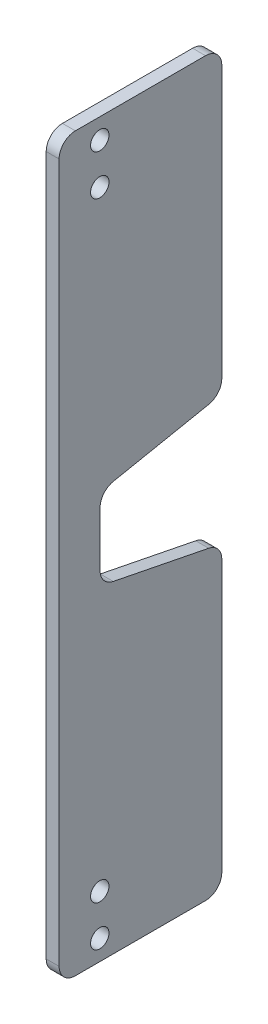
SolidWorks part; units mm, degrees
ref_plane "前视基准面" through (0, 0, 0) normal (0, 0, 1) x (1, 0, 0)
ref_plane "上视基准面" through (0, 0, 0) normal (0, 1, 0) x (1, 0, 0)
ref_plane "右视基准面" through (0, 0, 0) normal (1, 0, 0) x (0, 0, -1)
ref_plane "基准面4" through (-0.7938, 0, 0) normal (-1, 0, 0) x (0, -1, 0)
sketch "草图1" plane through (-0.7938, 0, 0) normal (-1, 0, 0) x (0, -1, 0)
  line L1 (38.795, 5) -> (12.795, 5)
  line L2 (10.795, 3) -> (10.795, -13)
  line L5 (10.795, 3) -> (55.77, 3) construction
  line L6 (55.77, 3) -> (55.77, -5.0783) construction
  line L7 (55.77, 3) -> (55.77, 5) construction
  line L13 (38.795, 5) -> (72.745, 5)
  line L15 (100.745, 3) -> (100.745, -13)
  line L18 (72.745, 5) -> (98.745, 5)
  line L19 (55.77, 5) -> (55.77, -5.0783) construction
  line L20 (55.77, -5.0783) -> (55.77, -0.0391) construction
  line L21 (55.77, -0.0391) -> (65.77, -0.0391) construction
  line L22 (72.112, -14.1547) -> (62.1308, -0.0391) construction
  line L31 (12.795, -15) -> (47.795, -15)
  line L32 (55.77, -0.0391) -> (50.77, -0.0391)
  line L33 (55.77, -0.0391) -> (60.77, -0.0391)
  line L34 (98.745, -15) -> (63.745, -15)
  line L37 (50.77, -0.0391) -> (47.795, -15)
  line L38 (60.77, -0.0391) -> (63.745, -15)
  arc A2 (12.795, 5) -> (10.795, 3) centre (12.795, 3) ccw
  arc A3 (10.795, -13) -> (12.795, -15) centre (12.795, -13) ccw
  circle A5 centre (18.295, 0) radius 1.1303
  circle A6 centre (13.295, 0) radius 1.1303
  arc A12 (98.745, 5) -> (100.745, 3) centre (98.745, 3) cw
  arc A13 (100.745, -13) -> (98.745, -15) centre (98.745, -13) cw
  circle A14 centre (98.245, 0) radius 1.1303
  circle A15 centre (93.245, 0) radius 1.1303
extrude "凸台-拉伸1" add sketch "草图1" against normal blind 1.588
fillet "圆角1" radius 2 1 edges at (0.0002, -50.77, -0.0391)
fillet "圆角2" radius 2 1 edges at (0.0003, -47.795, -15)
fillet "圆角3" radius 2 1 edges at (0.0002, -60.77, -0.0391)
fillet "圆角4" radius 2 1 edges at (0.0003, -63.745, -15)
